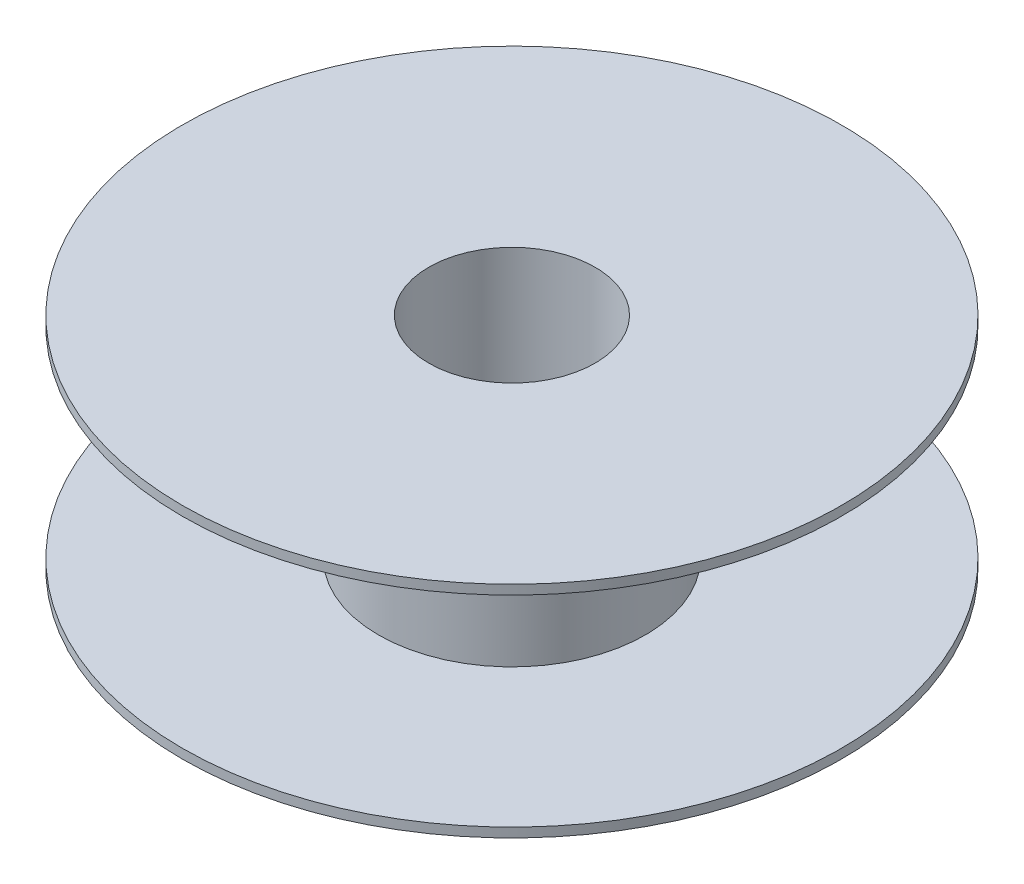
SolidWorks part; units mm, degrees
ref_plane "Plano frontal" through (0, 0, 0) normal (0, 0, 1) x (1, 0, 0)
ref_plane "Plano superior" through (0, 0, 0) normal (0, 1, 0) x (1, 0, 0)
ref_plane "Plano direito" through (0, 0, 0) normal (1, 0, 0) x (0, 0, -1)
sketch "Esboço1" plane through (0, 0, 0) normal (0, 0, 1) x (1, 0, 0)
  line L0 (26.5, 35) -> (26.5, -35)
  line L1 (26.5, -35) -> (105, -35)
  line L2 (105, -35) -> (105, -32)
  line L3 (105, -32) -> (42.5, -32)
  line L4 (42.5, -32) -> (42.5, 32)
  line L5 (42.5, 32) -> (105, 32)
  line L6 (105, 32) -> (105, 35)
  line L7 (105, 35) -> (26.5, 35)
  line L8 (0, 0) -> (22.4138, 0) construction
  line L9 (0, 23.2922) -> (0, 0) construction
  dimension "D1" = 3
  dimension "D2" = 70
  dimension "D3" = 210
  dimension "D4" = 85
  dimension "D5" = 53
revolve "Revolução1" add sketch "Esboço1" angle 360 about L9
